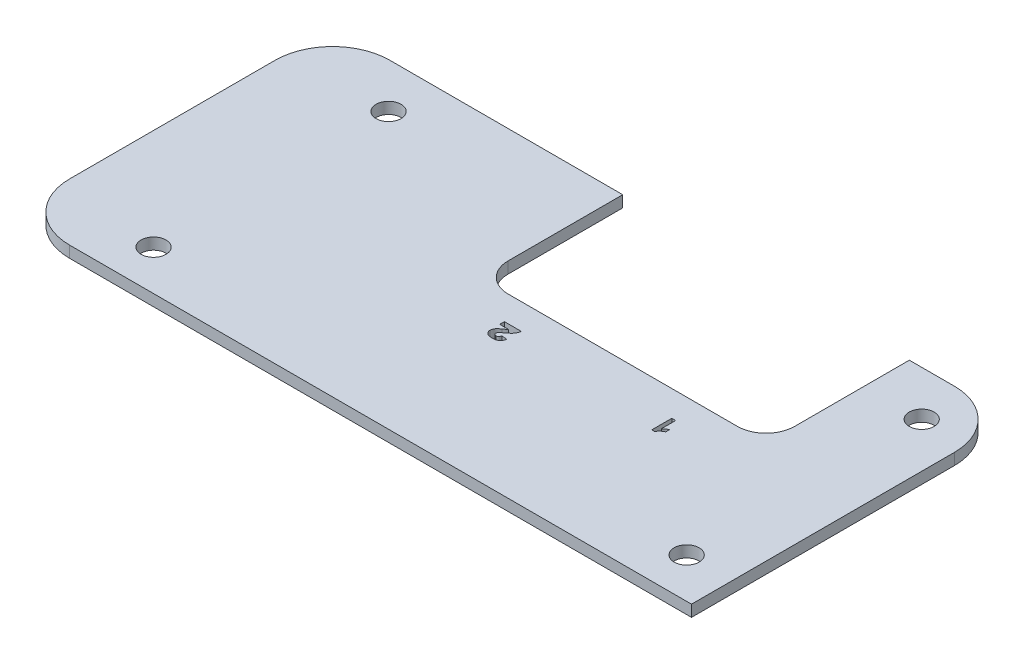
SolidWorks part; units mm, degrees
ref_plane "Alzado" through (0, 0, 0) normal (0, 0, 1) x (1, 0, 0)
ref_plane "Planta" through (0, 0, 0) normal (0, 1, 0) x (1, 0, 0)
ref_plane "Vista lateral" through (0, 0, 0) normal (1, 0, 0) x (0, 0, -1)
sketch "Croquis1" plane through (0, 0, 0) normal (0, 1, 0) x (1, 0, 0)
  line L0 (-59.2467, 17.9315) -> (-59.2467, -17.9315)
  line L1 (-49.2467, -27.9315) -> (-31.5006, -27.9315)
  line L2 (37.9141, -27.9315) -> (59.2467, -27.9315)
  line L3 (59.2467, -27.9315) -> (59.2467, 17.9315)
  line L4 (49.2467, 27.9315) -> (-49.2467, 27.9315)
  line L5 (-31.5006, -27.9315) -> (37.9141, -27.9315)
  arc A0 (-59.2467, -17.9315) -> (-49.2467, -27.9315) centre (-49.2467, -17.9315) ccw
  arc A1 (59.2467, 17.9315) -> (49.2467, 27.9315) centre (49.2467, 17.9315) ccw
  arc A2 (-49.2467, 27.9315) -> (-59.2467, 17.9315) centre (-49.2467, 17.9315) ccw
  circle A3 centre (51.3851, -20.9168) radius 2.175
  circle A4 centre (-41.6149, -20.9168) radius 2.175
  circle A5 centre (-41.6149, 20.0832) radius 2.175
  circle A6 centre (51.3851, 20.0832) radius 2.175
  dimension "D1" = 118.4933
  dimension "D2" = 55.8631
extrude "Saliente-Extruir1" add sketch "Croquis1" along normal blind 2
sketch "Croquis2" plane through (0, 2, 0) normal (0, 1, 0) x (1, 0, 0)
  line L0 (49.2467, 27.9315) -> (-49.2467, 27.9315) construction
  line L1 (41.3851, 27.9315) -> (-8.6149, 27.9315)
  line L2 (41.3851, 27.9315) -> (41.3851, 2.9315)
  line L3 (41.3851, 2.9315) -> (-8.6149, 2.9315)
  line L4 (-8.6149, 27.9315) -> (-8.6149, 2.9315)
  circle A0 centre (51.3851, 20.0832) radius 2.175 construction
  dimension "D1" = 10
  dimension "D2" = 50
  dimension "D3" = 25
extrude "Cortar-Extruir1" cut sketch "Croquis2" against normal up to surface (2 mm away) up to face at (-7.3311, 0, -2.8575)
fillet "Redondeo1" radius 5 2 edges at (41.3851, 1, -2.9315) (-8.6149, 1, -2.9315)
sketch "Croquis4" plane through (0, 0, 0) normal (0, -1, 0) x (1, 0, 0)
  line L0 (-3.6149, -2.9315) -> (36.3851, -2.9315) construction
  text T0 "1" font "Arial" height 3.5
  text T1 "2" font "Arial Black" height 3.5
  point P2 (3.3291, 1.4635)
  point P3 (0, 0)
  point P4 (0, 0)
  dimension "D1" = 4.5
  dimension "D2" = 4.5
  dimension "D3" = 28
extrude "Cortar-Extruir2" cut sketch "Croquis4" against normal up to surface (2 mm away) up to face at (3.6148, 2, -7.3477)
